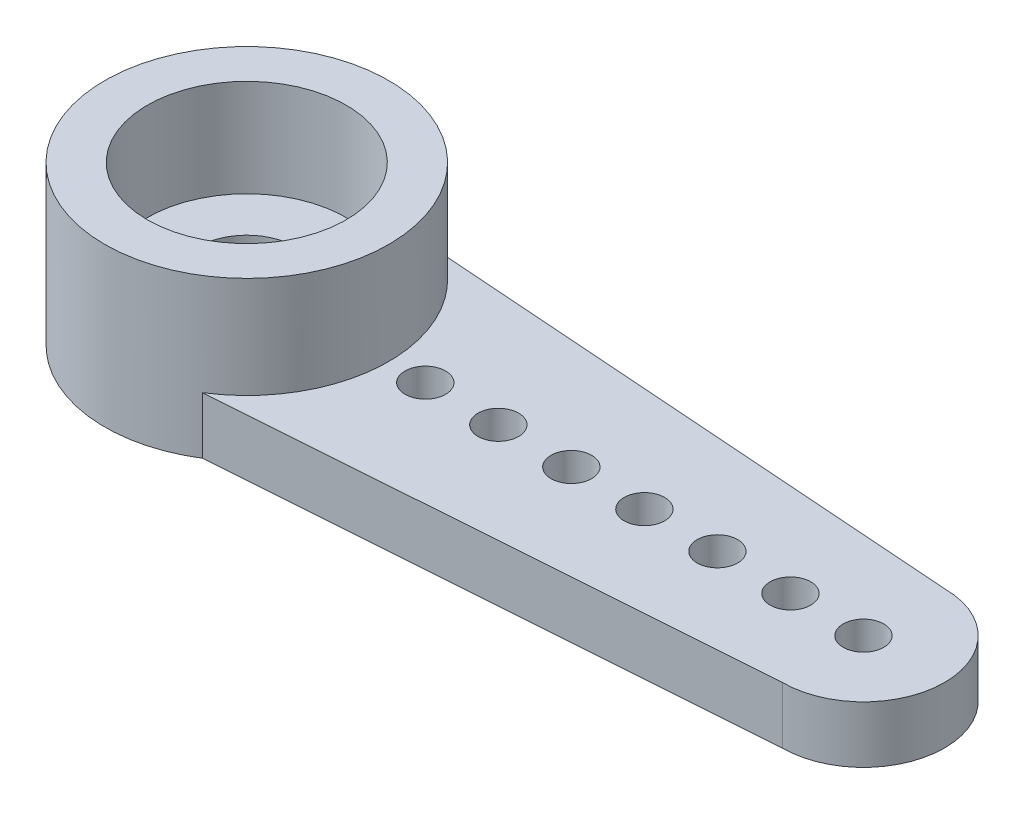
SolidWorks part; units mm, degrees
other "Camera1"
material "ABS"
ref_plane "Front Plane" through (0, 0, 0) normal (0, 0, 1) x (1, 0, 0)
ref_plane "Top Plane" through (0, 0, 0) normal (0, 1, 0) x (1, 0, 0)
ref_plane "Right Plane" through (0, 0, 0) normal (1, 0, 0) x (0, 0, -1)
sketch "Sketch1" plane through (0, 0, 0) normal (0, 1, 0) x (1, 0, 0)
  line L0 (-17.2, 0) -> (17.2, 0) construction
  line L1 (0, -8.35) -> (0, 8.35) construction
  line L2 (-15.2, 2) -> (-2, 2.95)
  line L3 (-15.2, -2) -> (-2, -2.95)
  line L4 (2, 6.35) -> (2, 3.5)
  line L5 (-2, 6.35) -> (-2, 2.95)
  line L6 (2, -6.35) -> (2, -3.5)
  line L7 (-2, -6.35) -> (-2, -2.95)
  line L8 (15.2, 2) -> (2, 3.5)
  line L9 (15.2, -2) -> (2, -3.5)
  circle A0 centre (0, 0) radius 3.5 construction
  arc A1 (-15.2, 2) -> (-15.2, -2) centre (-15.2, 0) ccw
  arc A2 (15.2, 2) -> (15.2, -2) centre (15.2, 0) cw
  arc A3 (2, 6.35) -> (-2, 6.35) centre (0, 6.35) ccw
  circle A4 centre (0, 6.35) radius 0.5
  circle A5 centre (0, 4.55) radius 0.5
  circle A6 centre (0, -4.55) radius 0.5
  circle A7 centre (0, -6.35) radius 0.5
  arc A8 (2, -6.35) -> (-2, -6.35) centre (0, -6.35) cw
  circle A10 centre (-15.2, 0) radius 0.5
  circle A11 centre (15.2, 0) radius 0.5
  circle A12 centre (-13.4, 0) radius 0.5
  circle A13 centre (-11.6, 0) radius 0.5
  circle A14 centre (-9.8, 0) radius 0.5
  circle A15 centre (-8, 0) radius 0.5
  circle A16 centre (-6.2, 0) radius 0.5
  circle A17 centre (-4.4, 0) radius 0.5
  circle A18 centre (13.4, 0) radius 0.5
  circle A19 centre (11.6, 0) radius 0.5
  circle A20 centre (9.8, 0) radius 0.5
  circle A21 centre (8, 0) radius 0.5
  circle A22 centre (6.2, 0) radius 0.5
  circle A23 centre (4.4, 0) radius 0.5
  point P5 (0, 0)
  point P8 (0, 0)
  point P25 (0, 6.85)
  point P26 (0, 4.05)
  dimension "D1" = 7
  dimension "D4" = 4
  dimension "D6" = 1
  dimension "D2" = 34.4
  dimension "D3" = 16.7
  dimension "D5" = 2
  dimension "D7" = 2.8
  dimension "D8" = 7
  dimension "D10" = 5.9
  dimension "D11" = 7
  dimension "D12" = 7
extrude "Boss-Extrude1" add sketch "Sketch1" along normal blind 1.4
sketch "Sketch2" plane through (0, 0, 0) normal (0, -1, 0) x (1, 0, 0)
  circle A0 centre (0, 0) radius 2.35
  dimension "D1" = 4.7
extrude "Cut-Extrude1" cut sketch "Sketch2" against normal blind 1
sketch "Sketch3" plane through (0, 1.4, 0) normal (0, 1, 0) x (1, 0, 0)
  circle A0 centre (0, 0) radius 2.45
  circle A1 centre (0, 0) radius 3.5
  dimension "D1" = 4.9
  dimension "D2" = 7
extrude "Boss-Extrude2" add sketch "Sketch3" along normal blind 2.5
sketch "Sketch4" plane through (0, 1.4, 0) normal (0, 1, 0) x (1, 0, 0)
  circle A0 centre (0, 0) radius 1.2
  dimension "D1" = 2.4
extrude "Cut-Extrude2" cut sketch "Sketch4" against normal through all
sketch "Sketch5" plane through (0, 1.4, 0) normal (0, 1, 0) x (1, 0, 0)
  circle A0 centre (0, 0) radius 1.2 construction
  circle A1 centre (0, 0) radius 2.45
  circle A2 centre (0, 0) radius 2.45
  circle A3 centre (0, 0) radius 1.2
  dimension "D1" = 0
extrude "Boss-Extrude3" add sketch "Sketch5" along normal blind 0.1
sketch "Sketch6" plane through (0, 0, 0) normal (0, -1, 0) x (1, 0, 0)
  line L0 (-2, -2.95) -> (-15.2, -2) construction
  line L1 (-1.8686, -2.9595) -> (-15.2, -2)
  line L2 (-15.2, 2) -> (-2, 2.95) construction
  line L3 (-15.2, 2) -> (-1.8686, 2.9595)
  line L4 (0, -9.3016) -> (0, 8.6978) construction
  line L5 (1.8686, -2.9595) -> (15.2, -2)
  line L6 (15.2, 2) -> (1.8686, 2.9595)
  line L8 (-17.8676, -8.836) -> (17.8676, -8.836)
  line L9 (-17.8676, -8.836) -> (-17.8676, 8.836)
  line L10 (-17.8676, 8.836) -> (17.8676, 8.836)
  line L11 (17.8676, -8.836) -> (17.8676, 8.836)
  line L12 (-17.8676, -8.836) -> (17.8676, 8.836) construction
  line L13 (-17.8676, 8.836) -> (17.8676, -8.836) construction
  arc A0 (-15.2, 2) -> (-15.2, -2) centre (-15.2, 0) ccw construction
  arc A1 (-15.2, 2) -> (-15.2, -2) centre (-15.2, 0) ccw
  circle A2 centre (0, 0) radius 3.5 construction
  arc A3 (1.8686, 2.9595) -> (-1.8686, 2.9595) centre (0, 0) ccw
  arc A4 (15.2, 2) -> (15.2, -2) centre (15.2, 0) cw
  arc A5 (-1.8686, -2.9595) -> (1.8686, -2.9595) centre (0, 0) ccw
extrude "Cut-Extrude4" cut sketch "Sketch6" against normal through all
sketch "Sketch7" plane through (0, 0, 0) normal (0, -1, 0) x (1, 0, 0)
  line L0 (0, 3.5) -> (-17.7318, 3.5)
  line L1 (-17.7318, 3.5) -> (-17.7318, -3.5)
  line L2 (-17.7318, -3.5) -> (0, -3.5)
  circle A0 centre (0, 0) radius 3.5 construction
  arc A1 (0, 3.5) -> (0, -3.5) centre (0, 0) ccw
extrude "Cut-Extrude5" cut sketch "Sketch7" against normal through all
